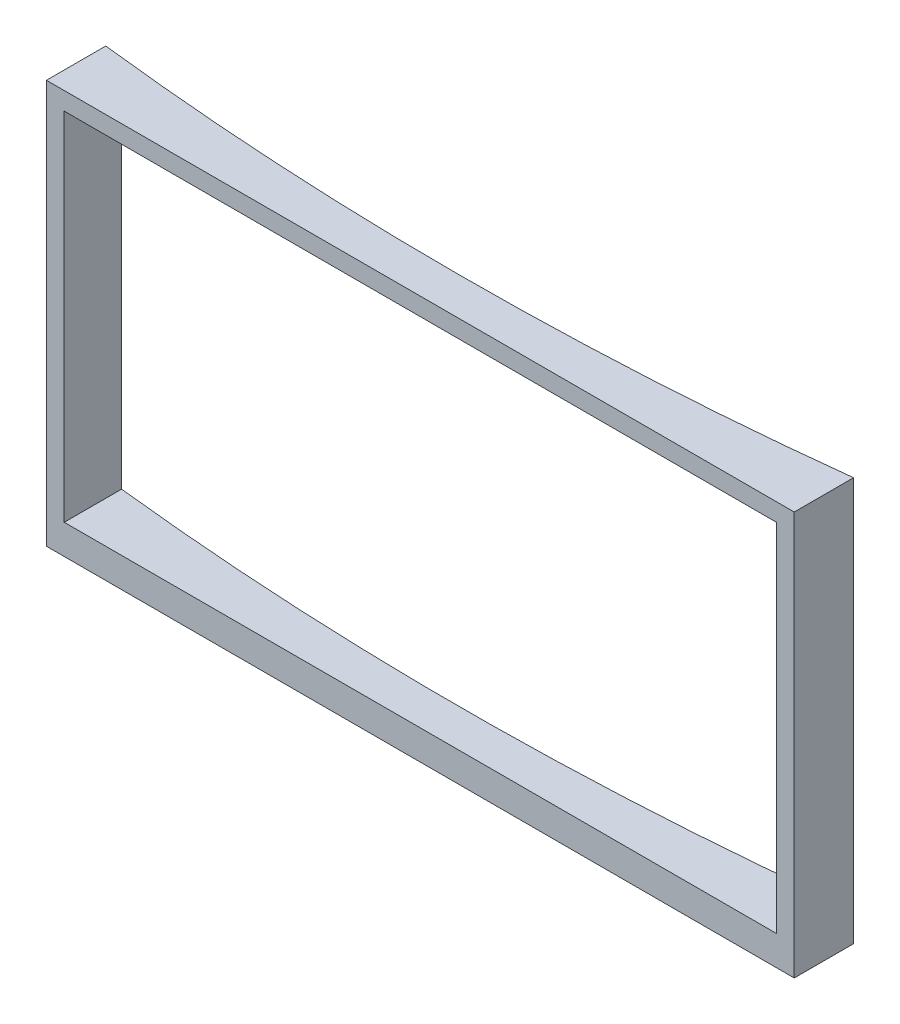
SolidWorks part; units mm, degrees
ref_plane "Front Plane" through (0, 0, 0) normal (0, 0, 1) x (1, 0, 0)
ref_plane "Top Plane" through (0, 0, 0) normal (0, 1, 0) x (1, 0, 0)
ref_plane "Right Plane" through (0, 0, 0) normal (1, 0, 0) x (0, 0, -1)
sketch "Sketch2" plane through (0, 0, 0) normal (0, 1, 0) x (1, 0, 0)
  line L0 (2590.5465, -3013.6099) -> (8890.5465, -3013.6099)
  line L1 (2590.5465, -3013.6099) -> (2590.5465, -2513.6099)
  line L2 (8890.5465, -3013.6099) -> (8890.5465, -2513.6099)
  arc A0 (2590.5465, -2513.6099) -> (8890.5465, -2513.6099) centre (5740.5465, 24805.3854) ccw
  point P3 (5740.5465, -3013.6099)
  dimension "D3" = 27500
  dimension "D1" = 6300
  dimension "D2" = 500
extrude "Boss-Extrude1" add sketch "Sketch2" along normal blind 3550
sketch "Sketch3" plane through (0, 0, 3013.6099) normal (0, 0, 1) x (1, 0, 0)
  line L0 (2590.5465, 3550) -> (2590.5465, 0) construction
  line L1 (2590.5465, 0) -> (8890.5465, 0) construction
  line L3 (2740.5465, 3250) -> (8740.5465, 3250)
  line L4 (8740.5465, 3250) -> (8740.5465, 250)
  line L5 (8740.5465, 250) -> (2740.5465, 250)
  line L6 (2740.5465, 250) -> (2740.5465, 3250)
  point P9 (5740.5465, 3250)
  dimension "D1" = 150
  dimension "D2" = 6000
  dimension "D3" = 6000
  dimension "D4" = 250
  dimension "D5" = 3000
  dimension "D6" = 3000
extrude "Cut-Extrude1" cut sketch "Sketch3" against normal blind 6000
sketch "Sketch4" plane through (0, 0, 3013.6099) normal (0, 0, 1) x (1, 0, 0)
  line L0 (2590.5465, 3400) -> (8890.5465, 3400)
  line L1 (8890.5465, 3400) -> (8890.5465, 3555.176)
  line L2 (8890.5465, 3555.176) -> (2590.5465, 3555.176)
  line L3 (2590.5465, 3555.176) -> (2590.5465, 3400)
  line L4 (8740.5465, 3250) -> (2740.5465, 3250) construction
  dimension "D1" = 150
extrude "Cut-Extrude2" cut sketch "Sketch4" against normal blind 1116
